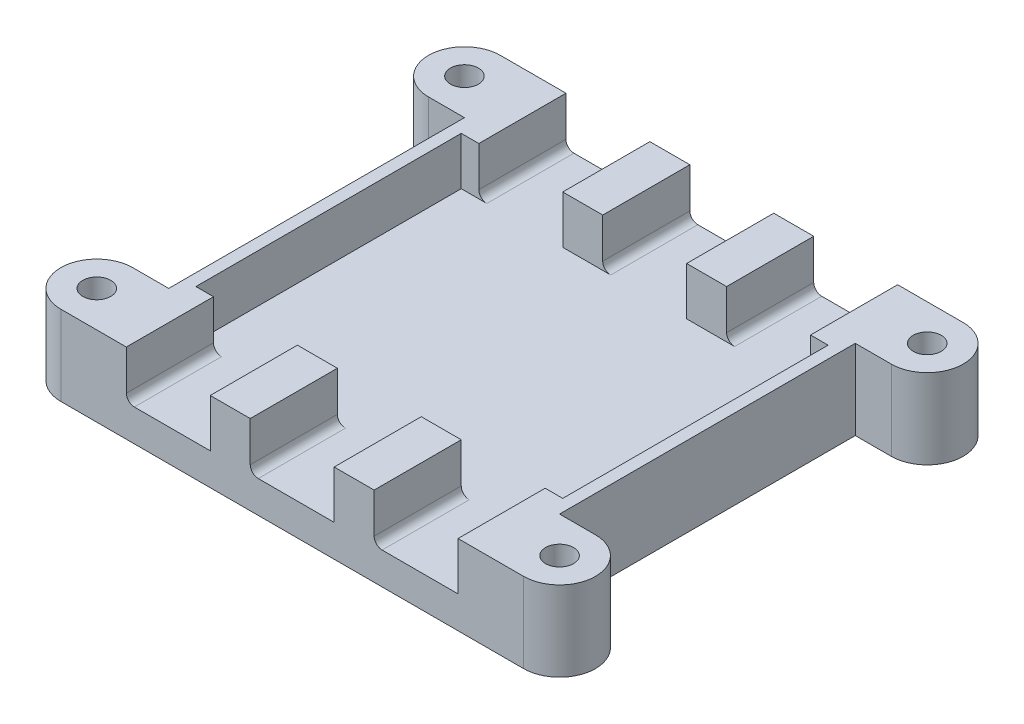
SolidWorks part; units mm, degrees
ref_plane "Front Plane" through (0, 0, 0) normal (0, 0, 1) x (1, 0, 0)
ref_plane "Top Plane" through (0, 0, 0) normal (0, 1, 0) x (1, 0, 0)
ref_plane "Right Plane" through (0, 0, 0) normal (1, 0, 0) x (0, 0, -1)
sketch "Sketch1" plane through (0, 0, 0) normal (0, 1, 0) x (1, 0, 0)
  line L0 (-22.95, 26) -> (-24.45, 26) construction
  line L1 (22.95, 16.6) -> (-22.95, 16.6)
  line L2 (22.95, 16.6) -> (22.95, -16.6)
  line L3 (22.95, -16.6) -> (-22.95, -16.6)
  line L4 (-22.95, 16.6) -> (-22.95, -16.6)
  line L5 (22.95, 16.6) -> (-22.95, -16.6) construction
  line L6 (22.95, -16.6) -> (-22.95, 16.6) construction
  line L7 (22.95, -26) -> (-22.95, -26)
  line L8 (22.95, -26) -> (22.95, 26)
  line L9 (22.95, 26) -> (-22.95, 26)
  line L10 (-22.95, -26) -> (-22.95, 26)
  line L11 (22.95, -26) -> (-22.95, 26) construction
  line L12 (22.95, 26) -> (-22.95, -26) construction
  line L13 (24.45, -27.5) -> (-24.45, -27.5)
  line L14 (24.45, -27.5) -> (24.45, 27.5)
  line L15 (24.45, 27.5) -> (-24.45, 27.5)
  line L16 (-24.45, -27.5) -> (-24.45, 27.5)
  line L17 (24.45, -27.5) -> (-24.45, 27.5) construction
  line L18 (24.45, 27.5) -> (-24.45, -27.5) construction
  line L19 (-22.95, 26) -> (-22.95, 27.5) construction
  point P0 (0, 0)
  point P6 (0, 0)
  point P11 (0, 0)
  dimension "D1" = 45.9
  dimension "D2" = 33.2
  dimension "D3" = 52
  dimension "D4" = 1.5
extrude "Boss-Extrude1" add sketch "Sketch1" along normal blind 4 contours L16 L13 L14 L15 L7 L10 L4 L9 L8 L2 | L10 L1 L8 L9 | L1 L4 L3 L2 | L10 L7 L8 L3
sketch "Sketch2" plane through (0, 4, 0) normal (0, 1, 0) x (1, 0, 0)
  line L0 (-24.45, -27.5) -> (-24.45, 27.5) construction
  line L1 (24.45, -16.6) -> (-24.45, -16.6)
  line L2 (24.45, -16.6) -> (24.45, 16.6)
  line L3 (24.45, 16.6) -> (-24.45, 16.6)
  line L4 (-24.45, -16.6) -> (-24.45, 16.6)
  line L5 (24.45, -16.6) -> (-24.45, 16.6) construction
  line L6 (24.45, 16.6) -> (-24.45, -16.6) construction
  line L7 (-22.95, 26) -> (-24.45, 26) construction
  line L8 (22.95, -26) -> (-22.95, -26)
  line L9 (22.95, -26) -> (22.95, 26)
  line L10 (22.95, 26) -> (-22.95, 26)
  line L11 (-22.95, -26) -> (-22.95, 26)
  line L12 (22.95, -26) -> (-22.95, 26) construction
  line L13 (22.95, 26) -> (-22.95, -26) construction
  line L14 (-22.95, 26) -> (-22.95, 27.5) construction
  line L15 (24.45, 27.5) -> (-24.45, 27.5) construction
  line L16 (0, 27.5) -> (0, -27.5) construction
  line L17 (24.45, -27.5) -> (-24.45, -27.5) construction
  line L18 (-15.5, 27.5) -> (-15.5, -27.5) construction
  line L19 (-5.25, 16.6) -> (5.25, 16.6)
  line L20 (-5.25, 16.6) -> (-5.25, 27.5)
  line L21 (-5.25, 27.5) -> (5.25, 27.5)
  line L22 (5.25, 16.6) -> (5.25, 27.5)
  line L23 (-5.25, 16.6) -> (5.25, 27.5) construction
  line L24 (-5.25, 27.5) -> (5.25, 16.6) construction
  line L25 (-24.45, 22.05) -> (24.45, 22.05) construction
  line L26 (24.45, -27.5) -> (24.45, 27.5) construction
  line L27 (20.75, 27.5) -> (10.25, 27.5)
  line L28 (-20.75, 16.6) -> (-10.25, 16.6)
  line L29 (-20.75, 16.6) -> (-20.75, 27.5)
  line L30 (-20.75, 27.5) -> (-10.25, 27.5)
  line L31 (-10.25, 16.6) -> (-10.25, 27.5)
  line L32 (-20.75, 16.6) -> (-10.25, 27.5) construction
  line L33 (-20.75, 27.5) -> (-10.25, 16.6) construction
  line L34 (20.75, 16.6) -> (20.75, 27.5)
  line L35 (10.25, 16.6) -> (10.25, 27.5)
  line L36 (-24.45, 0) -> (24.45, 0) construction
  line L37 (20.75, -16.6) -> (20.75, -27.5)
  line L38 (10.25, -16.6) -> (10.25, -27.5)
  line L39 (5.25, -16.6) -> (5.25, -27.5)
  line L40 (-5.25, -16.6) -> (-5.25, -27.5)
  line L41 (-10.25, -16.6) -> (-10.25, -27.5)
  line L42 (-20.75, -16.6) -> (-20.75, -27.5)
  point P0 (0, 0)
  point P8 (0, 0)
  point P21 (0, 22.05)
  point P32 (-15.5, 22.05)
  line M17 (-24.45, 27.5) -> (-24.45, -27.5)
  line M18 (-24.45, -27.5) -> (24.45, -27.5)
  line M19 (24.45, -27.5) -> (24.45, 27.5)
  line M20 (24.45, 27.5) -> (-24.45, 27.5)
  dimension "D1" = 33.2
  dimension "D2" = 1.5
  dimension "D3" = 10.5
  dimension "D4" = 5
extrude "Boss-Extrude2" add sketch "Sketch2" along normal blind 6 contours L10 L29 L3 L11 M20 M17 | L1 L11 L3 M17 | L42 L8 L11 L1 M17 M18 | L8 L41 L40 M18 | L8 L39 L38 M18 | L8 L37 L1 L9 M18 M19 | L9 L1 L3 M19 | L34 L10 L9 L3 M19 M20 | L10 L35 L22 M20 | L31 L10 L20 M20 | L31 L3 L20 L10 | L3 L35 L10 L22 | L1 L39 L8 L38 | L1 L41 L8 L40 | L3 L29 L10 L11 | L34 L3 L9 L10 | L1 L37 L8 L9 | L42 L1 L11 L8
sketch "Sketch4" plane through (0, 0, 0) normal (0, -1, 0) x (1, 0, 0)
  line L0 (-28.95, 27.5) -> (-24.45, 27.5)
  line L1 (-24.45, 27.5) -> (-24.45, -27.5) construction
  line L3 (-28.95, 18.5) -> (-24.45, 18.5)
  line L5 (0, 27.5) -> (0, -27.5) construction
  line L6 (24.45, 27.5) -> (-24.45, 27.5) construction
  line L7 (24.45, -27.5) -> (-24.45, -27.5) construction
  line L8 (-24.45, 0) -> (24.45, 0) construction
  line L9 (24.45, 27.5) -> (24.45, -27.5) construction
  line L10 (28.95, 27.5) -> (24.45, 27.5)
  line L11 (28.95, 18.5) -> (24.45, 18.5)
  line L12 (-28.95, -18.5) -> (-24.45, -18.5)
  line L13 (-28.95, -27.5) -> (-24.45, -27.5)
  line L14 (28.95, -27.5) -> (24.45, -27.5)
  line L15 (28.95, -18.5) -> (24.45, -18.5)
  circle A0 centre (-28.95, 23) radius 4.5
  circle A1 centre (-28.95, 23) radius 1.75
  circle A2 centre (28.95, 23) radius 1.75
  circle A3 centre (28.95, 23) radius 4.5
  circle A4 centre (-28.95, -23) radius 1.75
  circle A5 centre (-28.95, -23) radius 4.5
  circle A6 centre (28.95, -23) radius 1.75
  circle A7 centre (28.95, -23) radius 4.5
  line M8 (-24.45, 27.5) -> (-24.45, -27.5)
  line M10 (24.45, -27.5) -> (24.45, 27.5)
  dimension "D1" = 9
  dimension "D2" = 3.5
extrude "Boss-Extrude3" add sketch "Sketch4" against normal up to surface (10 mm away) contours A0 L0 M8 | A0 L3 M8 | A0 A1 | A3 L10 M10 | A3 A2 | L11 A3 M10 | A7 A6 | A7 L14 M10 | A7 L15 M10 | A5 L13 M8 | L12 A5 M8 | A5 A4 up to face at (-22.225, 10, 0)
fillet "Fillet1" radius 1 6 edges at (-20.75, 4, 22.05) (-5.25, 4, 22.05) (10.25, 4, 22.05) (10.25, 4, -22.05) (-5.25, 4, -22.05) (-20.75, 4, -22.05)
sketch "Sketch5" plane through (0, 0, 0) normal (0, -1, 0) x (1, 0, 0)
  line L0 (0, 27.5) -> (0, -27.5) construction
  line L1 (-28.95, 19.7091) -> (-26.1, 21.3546)
  line L2 (-26.1, 21.3546) -> (-26.1, 24.6454)
  line L3 (-26.1, 24.6454) -> (-28.95, 26.2909)
  line L4 (-28.95, 26.2909) -> (-31.8, 24.6454)
  line L5 (-31.8, 24.6454) -> (-31.8, 21.3546)
  line L6 (-31.8, 21.3546) -> (-28.95, 19.7091)
  line L7 (28.95, 27.5) -> (-28.95, 27.5) construction
  line L8 (28.95, -27.5) -> (-28.95, -27.5) construction
  line L9 (-24.45, 0) -> (24.45, 0) construction
  line L10 (-24.45, 18.5) -> (-24.45, -18.5) construction
  line L11 (24.45, 18.5) -> (24.45, -18.5) construction
  line L12 (31.8, 21.3546) -> (28.95, 19.7091)
  line L13 (31.8, 24.6454) -> (31.8, 21.3546)
  line L14 (28.95, 26.2909) -> (31.8, 24.6454)
  line L15 (26.1, 24.6454) -> (28.95, 26.2909)
  line L16 (26.1, 21.3546) -> (26.1, 24.6454)
  line L17 (28.95, 19.7091) -> (26.1, 21.3546)
  line L18 (31.8, -21.3546) -> (28.95, -19.7091)
  line L19 (31.8, -24.6454) -> (31.8, -21.3546)
  line L20 (28.95, -26.2909) -> (31.8, -24.6454)
  line L21 (26.1, -24.6454) -> (28.95, -26.2909)
  line L22 (26.1, -21.3546) -> (26.1, -24.6454)
  line L23 (28.95, -19.7091) -> (26.1, -21.3546)
  line L24 (-31.8, -21.3546) -> (-28.95, -19.7091)
  line L25 (-31.8, -24.6454) -> (-31.8, -21.3546)
  line L26 (-28.95, -26.2909) -> (-31.8, -24.6454)
  line L27 (-26.1, -24.6454) -> (-28.95, -26.2909)
  line L28 (-26.1, -21.3546) -> (-26.1, -24.6454)
  line L29 (-28.95, -19.7091) -> (-26.1, -21.3546)
  circle A0 centre (-28.95, 23) radius 2.85 construction
  dimension "D1" = 5.7
extrude "Cut-Extrude1" cut sketch "Sketch5" against normal blind 2.75
